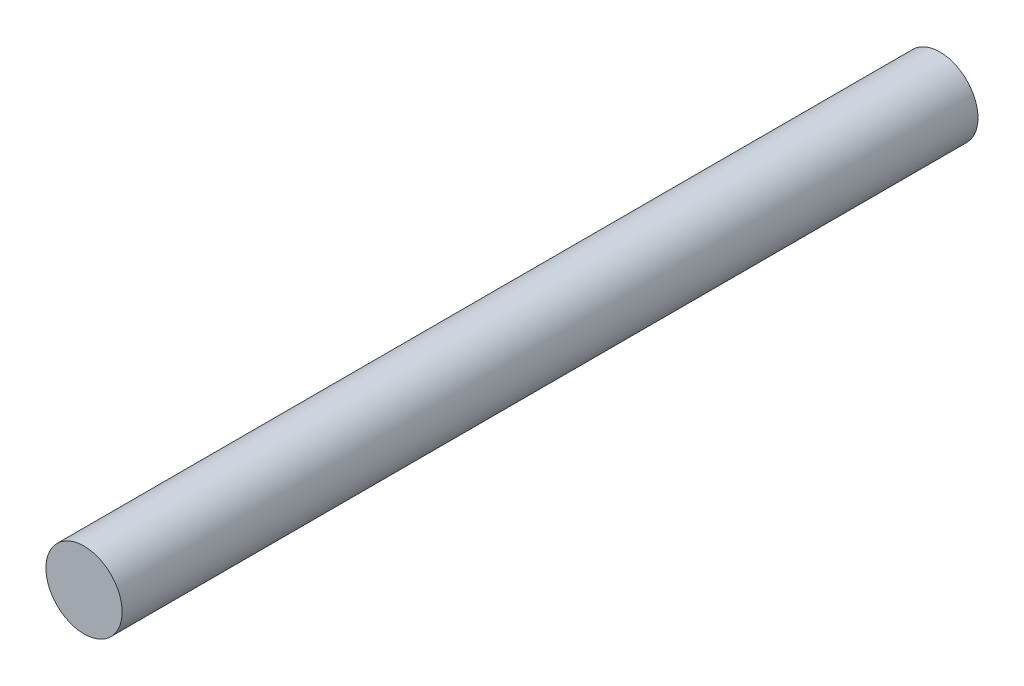
SolidWorks part; units mm, degrees
material "AISI 1010 Steel, hot rolled bar"
ref_plane "Front Plane" through (0, 0, 0) normal (0, 0, 1) x (1, 0, 0)
ref_plane "Top Plane" through (0, 0, 0) normal (0, 1, 0) x (1, 0, 0)
ref_plane "Right Plane" through (0, 0, 0) normal (1, 0, 0) x (0, 0, -1)
sketch "Sketch1" plane through (0, 0, 0) normal (0, 0, 1) x (1, 0, 0)
  circle A0 centre (0, 0) radius 4.7625
extrude "Boss-Extrude1" add sketch "Sketch1" along normal blind 107
